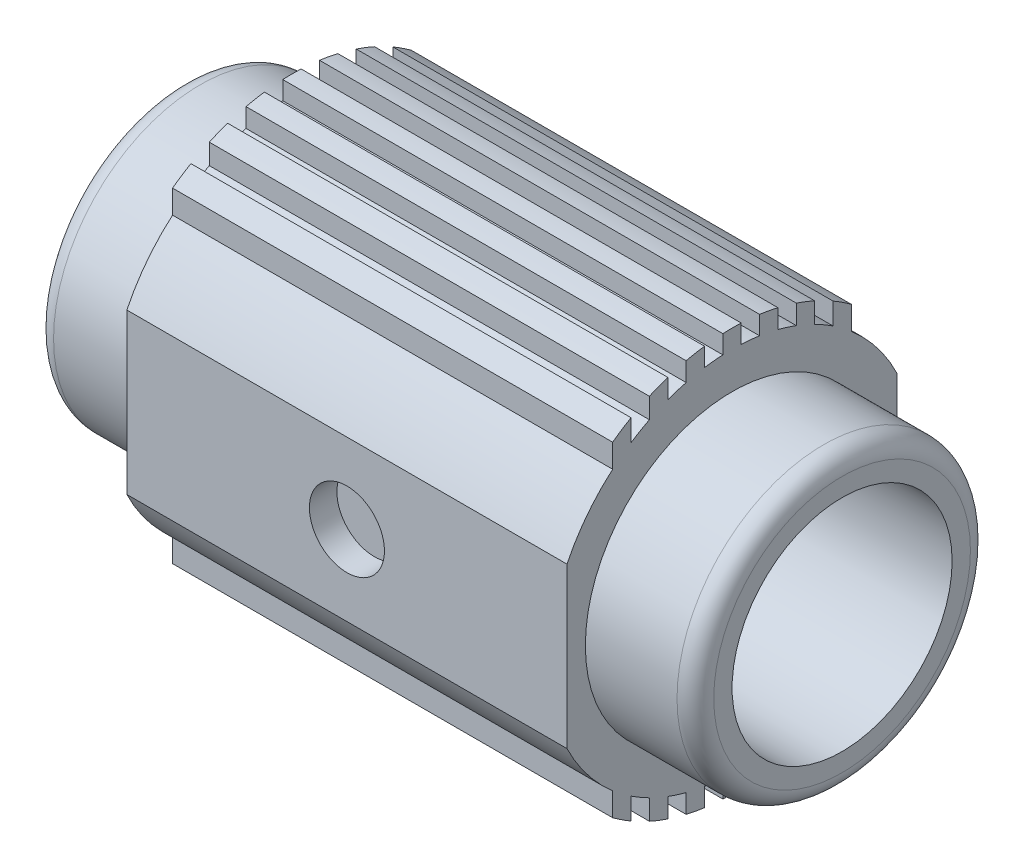
SolidWorks part; units mm, degrees
material "AISI 1035 Steel (SS)"
ref_plane "Front Plane" through (0, 0, 0) normal (0, 0, 1) x (1, 0, 0)
ref_plane "Top Plane" through (0, 0, 0) normal (0, 1, 0) x (1, 0, 0)
ref_plane "Right Plane" through (0, 0, 0) normal (1, 0, 0) x (0, 0, -1)
sketch "Sketch1" plane through (0, 0, 0) normal (1, 0, 0) x (0, 0, -1)
  line L2 (0.4039, 8.863) -> (0.4039, 8.0544)
  line L3 (-0.4039, -8.863) -> (-0.4039, -8.0544)
  line L4 (1.2116, 7.973) -> (1.2116, 8.7891)
  line L5 (-1.2116, -7.973) -> (-1.2116, -8.7891)
  line L6 (2.0193, 8.6394) -> (2.0193, 7.8076)
  line L7 (-2.0193, -8.6394) -> (-2.0193, -7.8076)
  line L8 (2.827, 7.5528) -> (2.827, 8.4098)
  line L9 (-2.827, -7.5528) -> (-2.827, -8.4098)
  line L10 (3.6347, 8.0935) -> (3.6347, 7.1989)
  line L11 (-3.6347, -8.0935) -> (-3.6347, -7.1989)
  line L12 (4.4425, 6.7306) -> (4.4425, 7.6799)
  line L13 (-4.4425, -6.7306) -> (-4.4425, -7.6799)
  line L14 (5.2502, 7.1521) -> (5.2502, 6.1214)
  line L15 (-5.2502, 7.1521) -> (-5.2502, 6.1214)
  line L16 (-5.2502, -7.1521) -> (-5.2502, -6.1214)
  line L17 (-4.4425, 6.7306) -> (-4.4425, 7.6799)
  line L18 (5.2502, -7.1521) -> (5.2502, -6.1214)
  line L19 (-3.6347, 8.0935) -> (-3.6347, 7.1989)
  line L20 (4.4425, -6.7306) -> (4.4425, -7.6799)
  line L21 (-2.827, 7.5528) -> (-2.827, 8.4098)
  line L22 (3.6347, -8.0935) -> (3.6347, -7.1989)
  line L23 (-2.0193, 8.6394) -> (-2.0193, 7.8076)
  line L24 (2.827, -7.5528) -> (2.827, -8.4098)
  line L25 (-1.2116, 7.973) -> (-1.2116, 8.7891)
  line L26 (2.0193, -8.6394) -> (2.0193, -7.8076)
  line L27 (-0.4039, 8.863) -> (-0.4039, 8.0544)
  line L28 (1.2116, -7.973) -> (1.2116, -8.7891)
  line L29 (0.4039, -8.863) -> (0.4039, -8.0544)
  line L30 (-7.2593, 3.5126) -> (-7.2593, -3.5126)
  line L31 (7.2593, 3.5126) -> (7.2593, -3.5126)
  arc A0 (-0.4039, 8.0544) -> (-1.2116, 7.973) centre (0, 0) ccw
  arc A1 (3.6347, 8.0935) -> (2.827, 8.4098) centre (0, 0) ccw
  arc A2 (-2.0193, 7.8076) -> (-2.827, 7.5528) centre (0, 0) ccw
  arc A3 (-3.6347, 7.1989) -> (-4.4425, 6.7306) centre (0, 0) ccw
  arc A4 (-5.2502, 6.1214) -> (-7.2593, 3.5126) centre (0, 0) ccw
  arc A5 (1.2116, 7.973) -> (0.4039, 8.0544) centre (0, 0) ccw
  arc A6 (2.827, 7.5528) -> (2.0193, 7.8076) centre (0, 0) ccw
  arc A7 (4.4425, 6.7306) -> (3.6347, 7.1989) centre (0, 0) ccw
  arc A8 (2.0193, 8.6394) -> (1.2116, 8.7891) centre (0, 0) ccw
  arc A9 (0.4039, 8.863) -> (-0.4039, 8.863) centre (0, 0) ccw
  arc A10 (-1.2116, 8.7891) -> (-2.0193, 8.6394) centre (0, 0) ccw
  arc A11 (-2.827, 8.4098) -> (-3.6347, 8.0935) centre (0, 0) ccw
  arc A12 (-4.4425, 7.6799) -> (-5.2502, 7.1521) centre (0, 0) ccw
  arc A13 (5.2502, 7.1521) -> (4.4425, 7.6799) centre (0, 0) ccw
  arc A14 (-5.2502, -7.1521) -> (-4.4425, -7.6799) centre (0, 0) ccw
  arc A15 (-3.6347, -8.0935) -> (-2.827, -8.4098) centre (0, 0) ccw
  arc A16 (-2.0193, -8.6394) -> (-1.2116, -8.7891) centre (0, 0) ccw
  arc A17 (-0.4039, -8.863) -> (0.4039, -8.863) centre (0, 0) ccw
  arc A18 (1.2116, -8.7891) -> (2.0193, -8.6394) centre (0, 0) ccw
  arc A19 (2.827, -8.4098) -> (3.6347, -8.0935) centre (0, 0) ccw
  arc A20 (4.4425, -7.6799) -> (5.2502, -7.1521) centre (0, 0) ccw
  arc A21 (5.2502, -6.1214) -> (7.2593, -3.5126) centre (0, 0) ccw
  arc A22 (3.6347, -7.1989) -> (4.4425, -6.7306) centre (0, 0) ccw
  arc A23 (2.0193, -7.8076) -> (2.827, -7.5528) centre (0, 0) ccw
  arc A24 (0.4039, -8.0544) -> (1.2116, -7.973) centre (0, 0) ccw
  arc A25 (-1.2116, -7.973) -> (-0.4039, -8.0544) centre (0, 0) ccw
  arc A26 (-2.827, -7.5528) -> (-2.0193, -7.8076) centre (0, 0) ccw
  arc A27 (-4.4425, -6.7306) -> (-3.6347, -7.1989) centre (0, 0) ccw
  arc A28 (-7.2593, -3.5126) -> (-5.2502, -6.1214) centre (0, 0) ccw
  arc A29 (7.2593, 3.5126) -> (5.2502, 6.1214) centre (0, 0) ccw
extrude "Boss-Extrude1" add sketch "Sketch1" along normal blind 9.6774 and the other way blind 9.6774
sketch "Sketch2" plane through (9.6774, 0, 0) normal (1, 0, 0) x (0, 0, -1)
  circle A0 centre (0, 0) radius 6.4516
extrude "Boss-Extrude2" add sketch "Sketch2" along normal blind 4.8387
sketch "Sketch3" plane through (-9.6774, 0, 0) normal (-1, 0, 0) x (0, 0, 1)
  circle A0 centre (0, 0) radius 6.4516
extrude "Boss-Extrude3" add sketch "Sketch3" along normal blind 4.8387
sketch "Sketch4" plane through (14.5161, 0, 0) normal (1, 0, 0) x (0, 0, -1)
  circle A0 centre (0, 0) radius 4.8387
extrude "Cut-Extrude1" cut sketch "Sketch4" against normal through all
fillet "Fillet1" radius 0.8077 2 edges at (-14.5161, 0, 6.4516) (14.5161, 0, -6.4516)
sketch "Sketch5" plane through (0, 0, 7.2593) normal (0, 0, 1) x (1, 0, 0)
  circle A0 centre (0, 0) radius 1.651
extrude "Cut-Extrude2" cut sketch "Sketch5" against normal blind 1.209
mirror "Mirror1" about plane through (0, 0, 0) normal (0, 0, 1) of "Cut-Extrude2"
